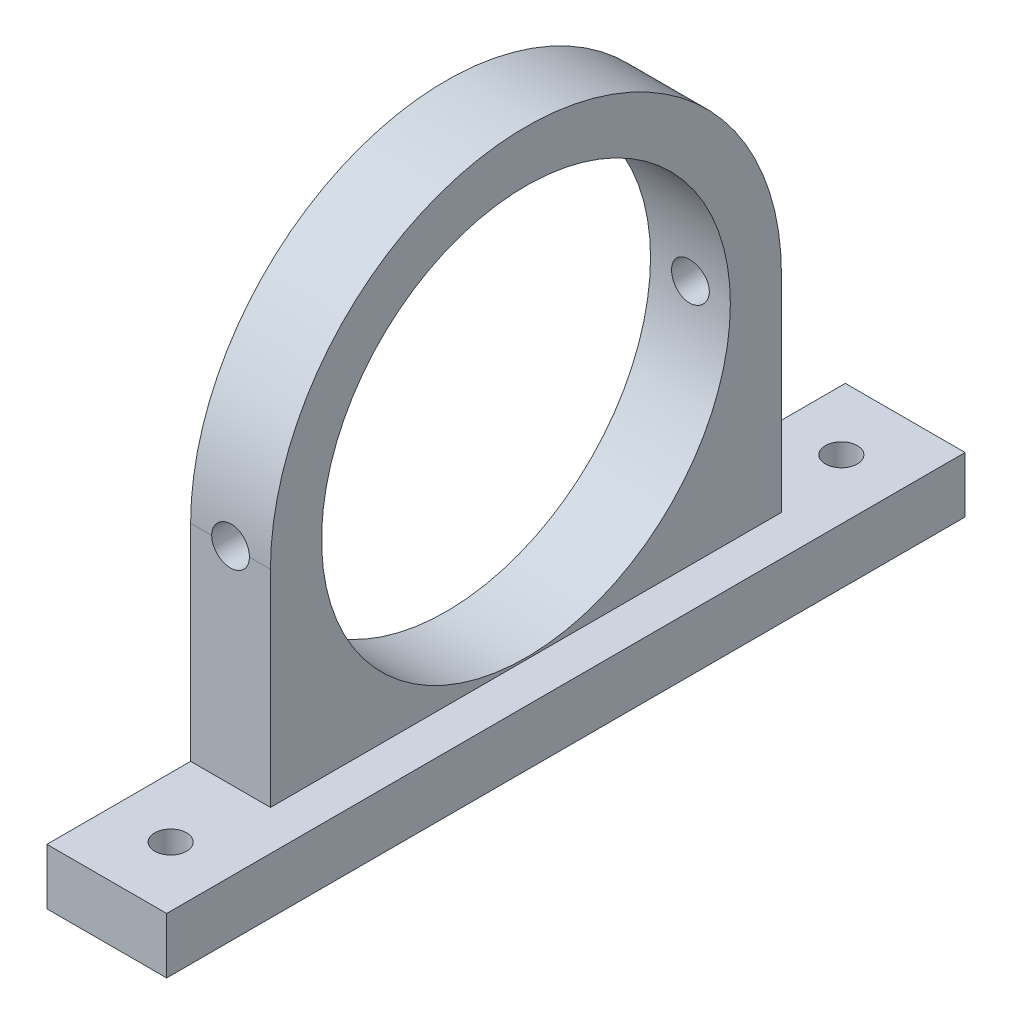
SolidWorks part; units mm, degrees
ref_plane "Front Plane" through (0, 0, 0) normal (0, 0, 1) x (1, 0, 0)
ref_plane "Top Plane" through (0, 0, 0) normal (0, 1, 0) x (1, 0, 0)
ref_plane "Right Plane" through (0, 0, 0) normal (1, 0, 0) x (0, 0, -1)
sketch "Sketch2" plane through (0, 0, 0) normal (1, 0, 0) x (0, 0, -1)
  line L0 (0, 0) -> (-23425.7277, 0) construction
  line L2 (0, -1000) -> (0, 49000) construction
  line L3 (31.75, 0) -> (-31.75, 0)
  line L4 (-31.75, 0) -> (-31.75, 4.445)
  line L5 (-31.75, 4.445) -> (-20.32, 4.445)
  line L6 (-20.32, 4.445) -> (-20.32, 20.85)
  line L7 (20.32, 4.445) -> (20.32, 20.85)
  line L8 (31.75, 0) -> (31.75, 4.445)
  line L9 (31.75, 4.445) -> (20.32, 4.445)
  line L10 (-20.32, 4.445) -> (20.32, 4.445)
  circle A0 centre (0, 20.85) radius 16.256
  arc A1 (-20.32, 20.85) -> (20.32, 20.85) centre (0, 20.85) cw
  point P17 (0, 0)
  dimension "D1" = 32.512
  dimension "D2" = 20.85
  dimension "D3" = 4.445
  dimension "D4" = 20.32
  dimension "D5" = 31.75
extrude "Boss-Extrude1" add sketch "Sketch2" along normal mid plane 6.35 contours L10 L5 L4 L3 L8 L9 | A1 L6 L10 L7 A0
sketch "Sketch3" plane through (3.175, 0, 0) normal (1, 0, 0) x (0, 0, -1)
  line L2 (31.75, 0) -> (31.75, 4.445) construction
  line L7 (31.75, 0) -> (-31.75, 0) construction
  line L12 (-31.75, 0) -> (-31.75, 4.445) construction
  line L13 (31.75, 0) -> (31.75, 4.445)
  line L14 (31.75, 0) -> (-31.75, 0)
  line L15 (-31.75, 0) -> (-31.75, 4.445)
  line L16 (-31.75, 4.445) -> (31.75, 4.445)
extrude "Boss-Extrude2" add sketch "Sketch3" along normal blind 3.175
hole_wizard "CSK for #0 Flat Head Machine Screw (100)1" positions "Sketch4" profile "Sketch5" countersink size "#0" standard "ANSI Inch" end condition through all
sketch "Sketch4" plane through (0, 0, -20.32) normal (0, 0, -1) x (-1, 0, 0)
  line L0 (-3.175, 20.85) -> (3.175, 20.85) construction
  point P0 (0, 20.85)
sketch "Sketch5" plane through (0, 20.85, -20.32) normal (1, 0, 0) x (0, 1, 0)
  line L0 (0, 0) -> (0, 52.07)
  line L1 (0, 52.07) -> (1.5, 52.07)
  line L2 (1.5, 52.07) -> (1.5, 0.0095)
  line L3 (1.5, 0.0095) -> (1.5113, 0)
  line L5 (1.5113, 0) -> (0, 0)
  line L6 (-1.5, 0.0095) -> (-1.5113, 0) construction
  line L11 (0, -6.35) -> (0, 107.95) construction
  dimension "Thru Hole Dia." = 3
  dimension "Thru Hole Depth" = 52.07
  dimension "Near C'Sink Dia." = 3.0226
  dimension "Near C'Sink Angle" = 100
sketch "Sketch6" plane through (0, 4.445, 0) normal (0, 1, 0) x (1, 0, 0)
  line L2 (-3.175, -31.75) -> (-3.175, -20.32) construction
  line L4 (6.35, -31.75) -> (-3.175, -31.75) construction
  circle A0 centre (1.5875, -26.67) radius 1.27
  dimension "D1" = 2.54
  dimension "D2" = 4.7625
  dimension "D3" = 5.08
extrude "Cut-Extrude1" cut sketch "Sketch6" against normal blind 6.35
mirror "Mirror2" about plane through (0, 0, 0) normal (0, 0, 1) of "Cut-Extrude1"
